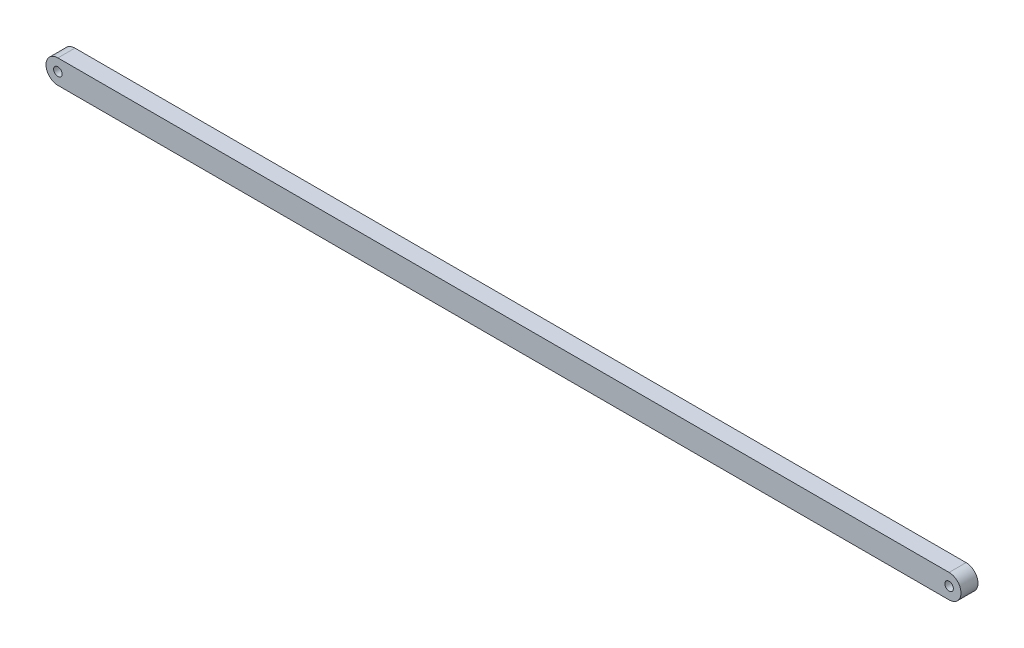
SolidWorks part; units mm, degrees
ref_plane "Front Plane" through (0, 0, 0) normal (0, 0, 1) x (1, 0, 0)
ref_plane "Top Plane" through (0, 0, 0) normal (0, 1, 0) x (1, 0, 0)
ref_plane "Right Plane" through (0, 0, 0) normal (1, 0, 0) x (0, 0, -1)
sketch "Sketch1" plane through (0, 0, 0) normal (0, 0, 1) x (1, 0, 0)
  line L0 (0, 0) -> (524, 0) construction
  line L1 (0, 7) -> (524, 7)
  line L2 (0, -7) -> (524, -7)
  arc A0 (0, 7) -> (0, -7) centre (0, 0) ccw
  arc A1 (524, -7) -> (524, 7) centre (524, 0) ccw
  circle A2 centre (0, 0) radius 2.5
  circle A3 centre (524, 0) radius 2.5
  point P3 (262, 0)
  dimension "D1" = 5
  dimension "D3" = 7
  dimension "D2" = 524
extrude "Boss-Extrude1" add sketch "Sketch1" along normal mid plane 10
